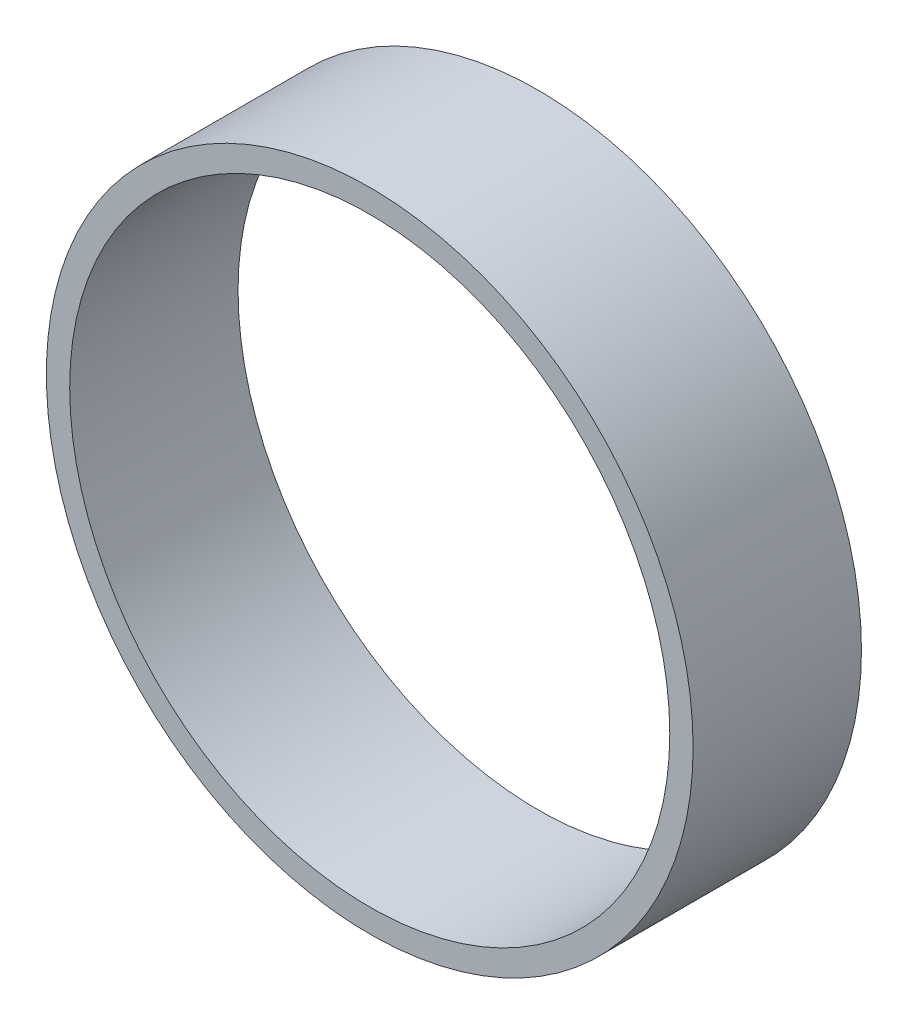
SolidWorks part; units mm, degrees
ref_plane "Front Plane" through (0, 0, 0) normal (0, 0, 1) x (1, 0, 0)
ref_plane "Top Plane" through (0, 0, 0) normal (0, 1, 0) x (1, 0, 0)
ref_plane "Right Plane" through (0, 0, 0) normal (1, 0, 0) x (0, 0, -1)
sketch "Sketch2" plane through (0, 0, 0) normal (0, 0, 1) x (1, 0, 0)
  circle A0 centre (0, 0) radius 45.72
  circle A1 centre (0, 0) radius 49.276
  dimension "D2" = 98.552
  dimension "D1" = 91.44
extrude "Boss-Extrude1" add sketch "Sketch2" along normal blind 25.654
